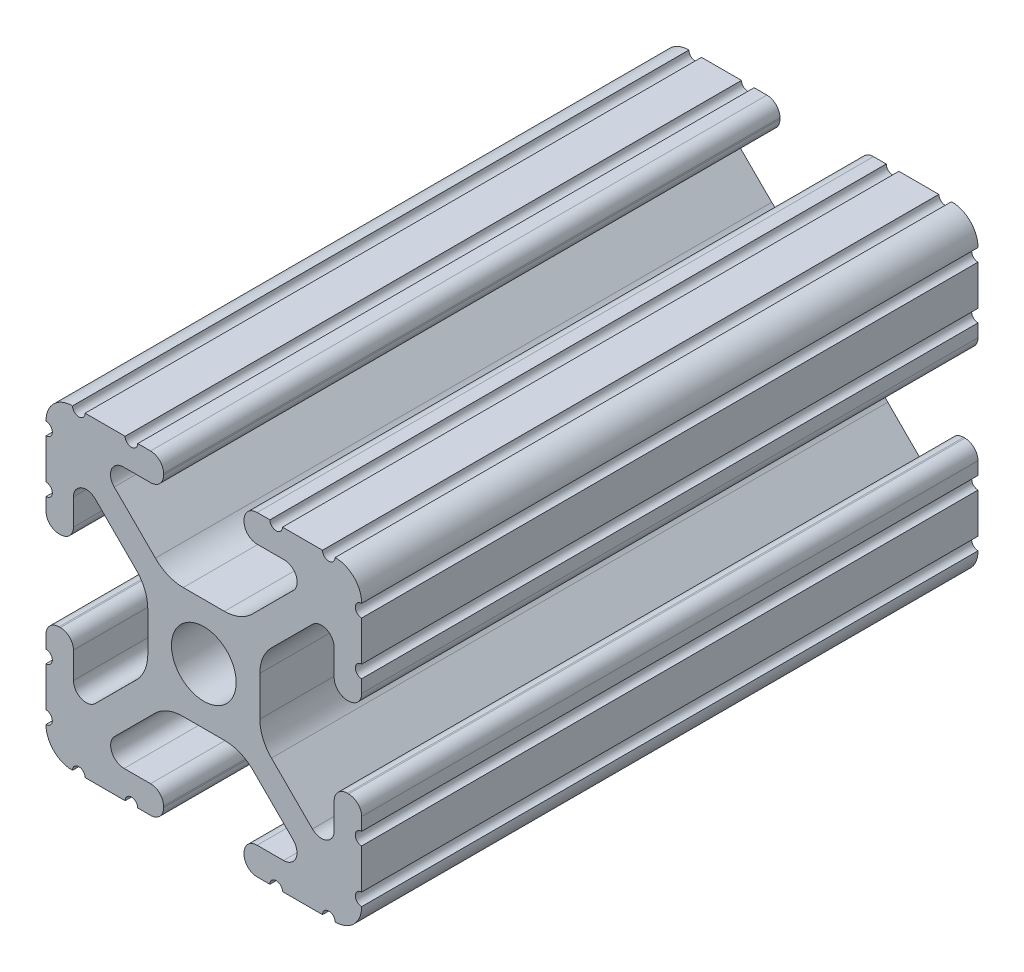
SolidWorks part; units mm, degrees
ref_plane "Front" through (0, 0, 0) normal (0, 0, 1) x (1, 0, 0)
ref_plane "Top" through (0, 0, 0) normal (0, 1, 0) x (1, 0, 0)
ref_plane "Right" through (0, 0, 0) normal (1, 0, 0) x (0, 0, -1)
sketch "Sketch1" plane through (0, 0, 0) normal (0, 0, 1) x (1, 0, 0)
  line L0 (-7.5107, 9.4563) -> (7.5107, 9.4563) construction
  line L1 (-7.4968, -9.4098) -> (7.4968, -9.4098) construction
  line L88 (-7.1797, -8.6452) -> (-3.9523, -5.4237)
  line L89 (-1.7093, -4.4958) -> (1.7093, -4.4958)
  line L90 (3.9523, -5.4237) -> (7.1797, -8.6452)
  line L91 (6.4164, -10.4902) -> (4.2875, -10.4902)
  line L92 (3.2385, -11.5392) -> (3.2385, -11.651)
  line L93 (4.2875, -12.7) -> (5.3171, -12.7)
  line L94 (6.3331, -12.7) -> (9.5504, -12.7)
  line L95 (12.7, -9.5504) -> (12.7, -6.3331)
  line L96 (12.7, -5.3171) -> (12.7, -4.2875)
  line L97 (11.651, -3.2385) -> (11.5392, -3.2385)
  line L98 (10.4902, -4.2875) -> (10.4902, -6.4021)
  line L99 (8.7371, -7.1294) -> (5.441, -3.8408)
  line L100 (4.5085, -1.5932) -> (4.5085, 1.5932)
  line L101 (5.441, 3.8408) -> (8.7371, 7.1294)
  line L102 (10.4902, 6.4021) -> (10.4902, 4.2875)
  line L103 (11.5392, 3.2385) -> (11.651, 3.2385)
  line L104 (12.7, 4.2875) -> (12.7, 5.3171)
  line L105 (12.7, 6.3331) -> (12.7, 9.5504)
  line L106 (9.5504, 12.7) -> (6.3331, 12.7)
  line L107 (5.3171, 12.7) -> (4.2875, 12.7)
  line L108 (3.2385, 11.651) -> (3.2385, 11.5392)
  line L109 (4.2875, 10.4902) -> (6.4768, 10.4902)
  line L110 (7.207, 8.7244) -> (3.8983, 5.4232)
  line L111 (1.6558, 4.4958) -> (-1.6558, 4.4958)
  line L112 (-3.8983, 5.4232) -> (-7.207, 8.7244)
  line L113 (-6.4768, 10.4902) -> (-4.2875, 10.4902)
  line L114 (-3.2385, 11.5392) -> (-3.2385, 11.651)
  line L115 (-4.2875, 12.7) -> (-5.3171, 12.7)
  line L116 (-6.3331, 12.7) -> (-9.5504, 12.7)
  line L117 (-12.7, 9.5504) -> (-12.7, 6.3331)
  line L118 (-12.7, 5.3171) -> (-12.7, 4.2875)
  line L119 (-11.651, 3.2385) -> (-11.5392, 3.2385)
  line L120 (-10.4902, 4.2875) -> (-10.4902, 6.4021)
  line L121 (-8.7371, 7.1294) -> (-5.441, 3.8408)
  line L122 (-4.5085, 1.5932) -> (-4.5085, -1.5932)
  line L123 (-5.441, -3.8408) -> (-8.7371, -7.1294)
  line L124 (-10.4902, -6.4021) -> (-10.4902, -4.2875)
  line L125 (-11.5392, -3.2385) -> (-11.651, -3.2385)
  line L126 (-12.7, -4.2875) -> (-12.7, -5.3171)
  line L127 (-12.7, -6.3331) -> (-12.7, -9.5504)
  line L128 (-9.5504, -12.7) -> (-6.3331, -12.7)
  line L129 (-5.3171, -12.7) -> (-4.2875, -12.7)
  line L130 (-3.2385, -11.651) -> (-3.2385, -11.5392)
  line L131 (-4.2875, -10.4902) -> (-6.4164, -10.4902)
  circle A1 centre (0, 0) radius 2.6035
  arc A104 (-7.1797, -8.6452) -> (-6.4164, -10.4902) centre (-6.4164, -9.4098) ccw
  arc A105 (-1.7093, -4.4958) -> (-3.9523, -5.4237) centre (-1.7093, -7.6708) ccw
  arc A106 (3.9523, -5.4237) -> (1.7093, -4.4958) centre (1.7093, -7.6708) ccw
  arc A107 (6.4164, -10.4902) -> (7.1797, -8.6452) centre (6.4164, -9.4098) ccw
  arc A108 (4.2875, -10.4902) -> (3.2385, -11.5392) centre (4.2875, -11.5392) ccw
  arc A109 (3.2385, -11.651) -> (4.2875, -12.7) centre (4.2875, -11.651) ccw
  arc A110 (6.3331, -12.7) -> (5.3171, -12.7) centre (5.8251, -12.7) ccw
  arc A111 (10.5664, -12.6998) -> (9.5504, -12.7) centre (10.0584, -12.7) ccw
  arc A112 (10.5664, -12.6998) -> (12.6998, -10.5664) centre (10.5918, -10.5918) ccw
  arc A113 (12.7, -9.5504) -> (12.6998, -10.5664) centre (12.7, -10.0584) ccw
  arc A114 (12.7, -5.3171) -> (12.7, -6.3331) centre (12.7, -5.8251) ccw
  arc A115 (12.7, -4.2875) -> (11.651, -3.2385) centre (11.651, -4.2875) ccw
  arc A116 (11.5392, -3.2385) -> (10.4902, -4.2875) centre (11.5392, -4.2875) ccw
  arc A117 (8.7371, -7.1294) -> (10.4902, -6.4021) centre (9.4628, -6.4021) ccw
  arc A118 (4.5085, -1.5932) -> (5.441, -3.8408) centre (7.6835, -1.5932) ccw
  arc A119 (5.441, 3.8408) -> (4.5085, 1.5932) centre (7.6835, 1.5932) ccw
  arc A120 (10.4902, 6.4021) -> (8.7371, 7.1294) centre (9.4628, 6.4021) ccw
  arc A121 (10.4902, 4.2875) -> (11.5392, 3.2385) centre (11.5392, 4.2875) ccw
  arc A122 (11.651, 3.2385) -> (12.7, 4.2875) centre (11.651, 4.2875) ccw
  arc A123 (12.7, 6.3331) -> (12.7, 5.3171) centre (12.7, 5.8251) ccw
  arc A124 (12.6998, 10.5664) -> (12.7, 9.5504) centre (12.7, 10.0584) ccw
  arc A125 (12.6998, 10.5664) -> (10.5664, 12.6998) centre (10.5918, 10.5918) ccw
  arc A126 (9.5504, 12.7) -> (10.5664, 12.6998) centre (10.0584, 12.7) ccw
  arc A127 (5.3171, 12.7) -> (6.3331, 12.7) centre (5.8251, 12.7) ccw
  arc A128 (4.2875, 12.7) -> (3.2385, 11.651) centre (4.2875, 11.651) ccw
  arc A129 (3.2385, 11.5392) -> (4.2875, 10.4902) centre (4.2875, 11.5392) ccw
  arc A130 (7.207, 8.7244) -> (6.4768, 10.4902) centre (6.4768, 9.4563) ccw
  arc A131 (1.6558, 4.4958) -> (3.8983, 5.4232) centre (1.6558, 7.6708) ccw
  arc A132 (-3.8983, 5.4232) -> (-1.6558, 4.4958) centre (-1.6558, 7.6708) ccw
  arc A133 (-6.4768, 10.4902) -> (-7.207, 8.7244) centre (-6.4768, 9.4563) ccw
  arc A134 (-4.2875, 10.4902) -> (-3.2385, 11.5392) centre (-4.2875, 11.5392) ccw
  arc A135 (-3.2385, 11.651) -> (-4.2875, 12.7) centre (-4.2875, 11.651) ccw
  arc A136 (-6.3331, 12.7) -> (-5.3171, 12.7) centre (-5.8251, 12.7) ccw
  arc A137 (-10.5664, 12.6998) -> (-9.5504, 12.7) centre (-10.0584, 12.7) ccw
  arc A138 (-10.5664, 12.6998) -> (-12.6998, 10.5664) centre (-10.5918, 10.5918) ccw
  arc A139 (-12.7, 9.5504) -> (-12.6998, 10.5664) centre (-12.7, 10.0584) ccw
  arc A140 (-12.7, 5.3171) -> (-12.7, 6.3331) centre (-12.7, 5.8251) ccw
  arc A141 (-12.7, 4.2875) -> (-11.651, 3.2385) centre (-11.651, 4.2875) ccw
  arc A142 (-11.5392, 3.2385) -> (-10.4902, 4.2875) centre (-11.5392, 4.2875) ccw
  arc A143 (-8.7371, 7.1294) -> (-10.4902, 6.4021) centre (-9.4628, 6.4021) ccw
  arc A144 (-4.5085, 1.5932) -> (-5.441, 3.8408) centre (-7.6835, 1.5932) ccw
  arc A145 (-5.441, -3.8408) -> (-4.5085, -1.5932) centre (-7.6835, -1.5932) ccw
  arc A146 (-10.4902, -6.4021) -> (-8.7371, -7.1294) centre (-9.4628, -6.4021) ccw
  arc A147 (-10.4902, -4.2875) -> (-11.5392, -3.2385) centre (-11.5392, -4.2875) ccw
  arc A148 (-11.651, -3.2385) -> (-12.7, -4.2875) centre (-11.651, -4.2875) ccw
  arc A149 (-12.7, -6.3331) -> (-12.7, -5.3171) centre (-12.7, -5.8251) ccw
  arc A150 (-12.6998, -10.5664) -> (-12.7, -9.5504) centre (-12.7, -10.0584) ccw
  arc A151 (-12.6998, -10.5664) -> (-10.5664, -12.6998) centre (-10.5918, -10.5918) ccw
  arc A152 (-9.5504, -12.7) -> (-10.5664, -12.6998) centre (-10.0584, -12.7) ccw
  arc A153 (-5.3171, -12.7) -> (-6.3331, -12.7) centre (-5.8251, -12.7) ccw
  arc A154 (-4.2875, -12.7) -> (-3.2385, -11.651) centre (-4.2875, -11.651) ccw
  arc A155 (-3.2385, -11.5392) -> (-4.2875, -10.4902) centre (-4.2875, -11.5392) ccw
extrude "Boss-Extrude1" add sketch "Sketch1" along normal mid plane 914.4
sketch "Sketch3" plane through (-12.7, 0, 0) normal (-1, 0, 0) x (0, 0, 1)
  line L0 (-203.2, -25.4) -> (-203.2, 21.1581) construction
  line L1 (-203.2, -27.5528) -> (-203.2, 21.1581)
  line L2 (-203.2, 21.1581) -> (-461.0909, 21.1581)
  line L3 (-461.0909, 21.1581) -> (-461.0909, -25.4)
  line L4 (-461.0909, -25.4) -> (-203.2, -27.5528)
extrude "Cut-Extrude2" cut sketch "Sketch3" against normal blind 26.924 and the other way blind 4.318
sketch "Sketch4" plane through (12.7, 0, 0) normal (1, 0, 0) x (0, 0, -1)
  line L0 (144.6511, 29.7946) -> (144.6511, -37.2673) construction
  line L1 (144.6511, 14.6686) -> (144.6511, -33.4545)
  line L2 (144.6511, -33.4545) -> (-421.9141, -33.4545)
  line L4 (144.6511, 14.6686) -> (-421.9141, 14.6686)
  line L5 (-421.9141, 14.6686) -> (-459.7909, 14.6686)
  line L6 (194.2521, 13.1549) -> (204.3187, 13.1549)
  line L7 (194.2521, 13.1549) -> (194.2521, -13.076)
  line L8 (194.2521, -13.076) -> (204.3187, -13.076)
  line L9 (204.3187, 13.1549) -> (204.3187, -13.076)
  line L14 (-459.7909, 14.6686) -> (-459.7909, -33.4545)
  line L15 (-459.7909, -33.4545) -> (-421.9141, -33.4545)
extrude "Cut-Extrude3" cut sketch "Sketch4" against normal through all
